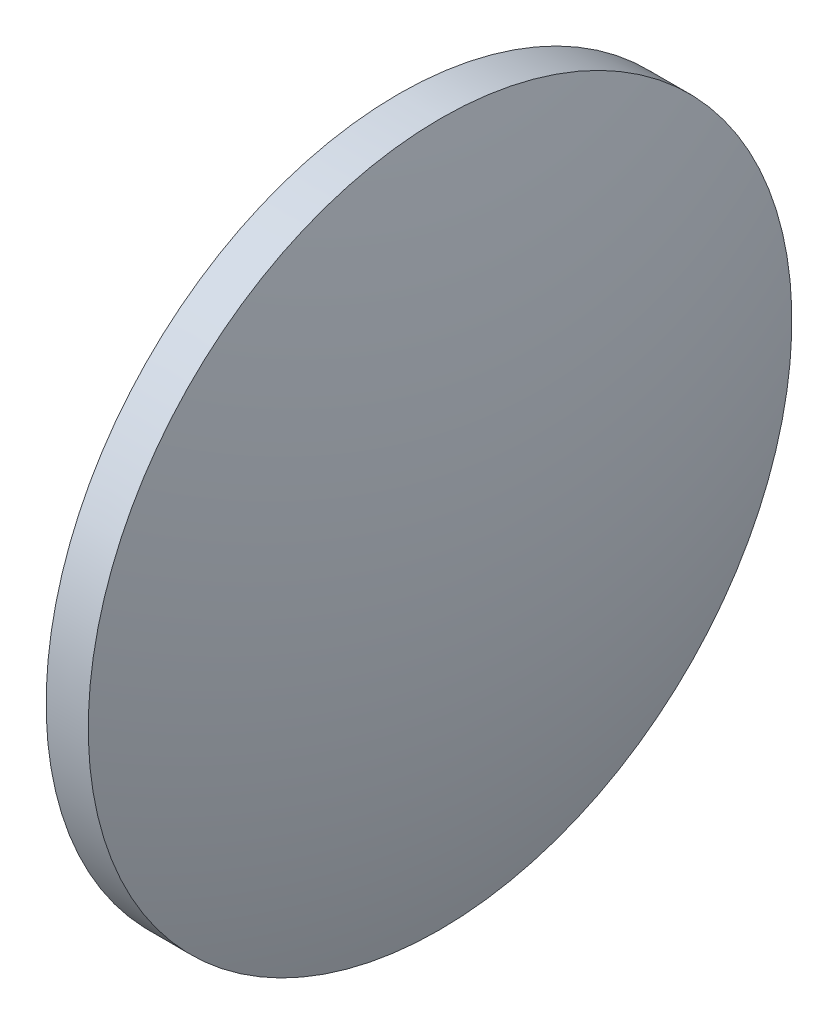
SolidWorks part; units mm, degrees
ref_plane "前视基准面" through (0, 0, 0) normal (0, 0, 1) x (1, 0, 0)
ref_plane "上视基准面" through (0, 0, 0) normal (0, 1, 0) x (1, 0, 0)
ref_plane "右视基准面" through (0, 0, 0) normal (1, 0, 0) x (0, 0, -1)
sketch "草图1" plane through (0, 0, 0) normal (0, 0, 1) x (1, 0, 0)
  line L0 (448.9498, -36.1502) -> (470.0768, -36.1912) construction
  line L1 (453.5977, -36.1592) -> (453.5977, -11.1592)
  line L2 (453.5977, -11.1592) -> (456.5977, -11.1592)
  line L3 (460.4677, -36.1725) -> (453.5977, -36.1592)
  arc A0 (460.4677, -36.1725) -> (456.5977, -11.1592) centre (377.7833, -36.1592) ccw
revolve "旋转1" add sketch "草图1" angle 360 about L0
